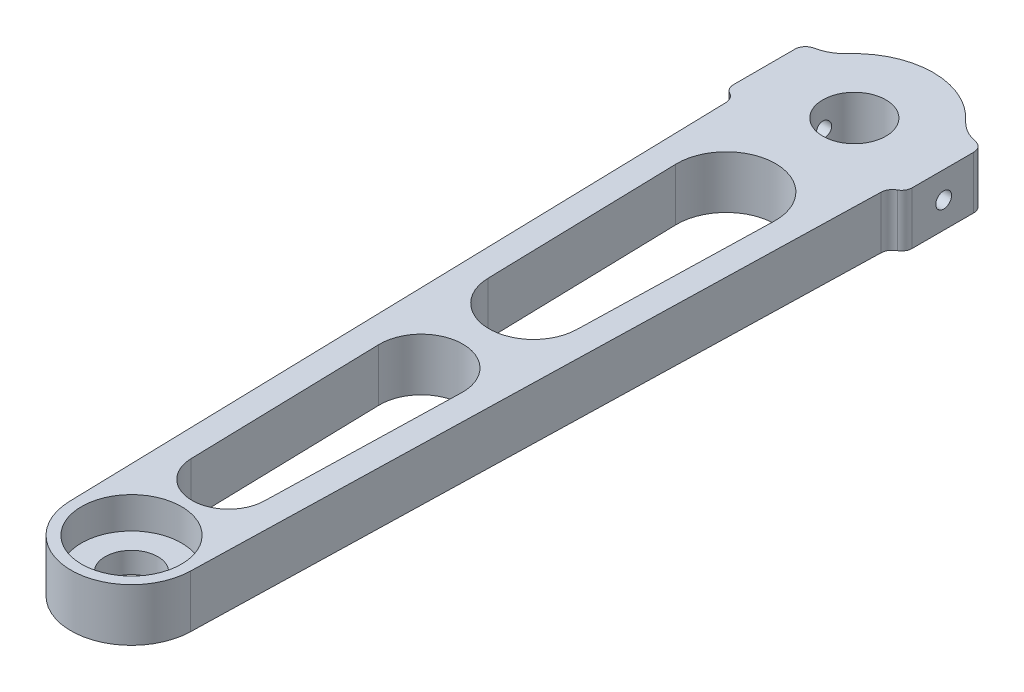
SolidWorks part; units mm, degrees
material "6061 Alloy"
ref_plane "Front Plane" through (0, 0, 0) normal (0, 0, 1) x (1, 0, 0)
ref_plane "Top Plane" through (0, 0, 0) normal (0, 1, 0) x (1, 0, 0)
ref_plane "Right Plane" through (0, 0, 0) normal (1, 0, 0) x (0, 0, -1)
sketch "Sketch1" plane through (0, 0, 0) normal (0, 1, 0) x (1, 0, 0)
  line L0 (-14.7584, -9.6805) -> (-11.4963, -137.7927)
  line L1 (14.7584, -9.6805) -> (11.4963, -137.7927)
  line L3 (-16.9951, 7.5) -> (-16.9951, -7.5)
  line L4 (16.9951, 7.5) -> (16.9951, -7.5)
  line L5 (-14.7584, -9.6805) -> (-14.9951, -0.3818) construction
  line L6 (14.7584, -9.6805) -> (14.9951, -0.3818) construction
  circle A0 centre (0, 0) radius 6
  arc A2 (-11.4963, -137.7927) -> (11.4963, -137.7927) centre (0, -137.5) ccw
  circle A3 centre (0, -137.5) radius 5
  arc A4 (-16.9951, -7.5) -> (-14.7584, -9.6805) centre (-16.9951, -9.7375) cw
  arc A5 (-16.9951, 7.5) -> (-11.2701, 9.8987) centre (-16.9951, 15.5313) ccw
  arc A8 (16.9951, 7.5) -> (11.2762, 9.8918) centre (16.9951, 15.5331) cw
  arc A9 (16.9951, -7.5) -> (14.7584, -9.6805) centre (16.9951, -9.7375) ccw
  arc A11 (14.9951, -0.3818) -> (-14.9951, -0.3818) centre (0, 0) ccw construction
  arc A12 (11.2762, 9.8918) -> (-11.2701, 9.8987) centre (0, 0) ccw
  point P14 (-16.9951, 0)
  point P25 (16.9951, 0)
  dimension "D1" = 12
  dimension "D2" = 2
  dimension "D3" = 23
  dimension "D5" = 10
  dimension "D9" = 30
  dimension "D4" = 137.5
  dimension "D7" = 15
  dimension "D8" = 15
  dimension "D11" = 2
extrude "Boss-Extrude1" add sketch "Sketch1" along normal blind 10
sketch "Sketch2" plane through (0, 10, 0) normal (0, 1, 0) x (1, 0, 0)
  circle A0 centre (0, -137.5) radius 9.5
  dimension "D1" = 19
extrude "Cut-Extrude1" cut sketch "Sketch2" against normal blind 6
sketch "Sketch4" plane through (0, 0, 0) normal (0, 1, 0) x (1, 0, 0)
  line L0 (-9.3764, -24.6182) -> (-8.4438, -61.2449)
  line L1 (9.3764, -24.6182) -> (8.4438, -61.2449)
  line L3 (-14.7584, -9.6805) -> (-11.4963, -137.7927) construction
  line L4 (0, -24.3794) -> (0, -61.0299) construction
  line L5 (-7.9005, -82.5806) -> (-6.9679, -119.2073)
  line L6 (7.9005, -82.5806) -> (6.9679, -119.2073)
  line L7 (0, -82.3794) -> (0, -119.0299) construction
  arc A0 (9.3764, -24.6182) -> (-9.3764, -24.6182) centre (0, -24.3794) ccw
  arc A1 (-8.4438, -61.2449) -> (8.4438, -61.2449) centre (0, -61.0299) ccw
  arc A2 (7.9005, -82.5806) -> (-7.9005, -82.5806) centre (0, -82.3794) ccw
  arc A3 (-6.9679, -119.2073) -> (6.9679, -119.2073) centre (0, -119.0299) ccw
  circle A5 centre (0, -137.5) radius 5 construction
  point P12 (0, -15)
  point P16 (0, -69.4764)
  point P20 (0, -74.4764)
  point P21 (0, -126)
  dimension "D1" = 15
  dimension "D2" = 5
  dimension "D3" = 11.5
  dimension "D5" = 5
extrude "Cut-Extrude3" cut sketch "Sketch4" along normal through all
fillet "Fillet1" radius 2 4 edges at (-16.9951, 5, -7.5) (-16.9951, 5, 7.5) (16.9951, 5, -7.5) (16.9951, 5, 7.5)
hole_wizard "M4 Tapped Hole1" positions "Sketch6" profile "Sketch7" tap size "M4" standard "ISO" end condition through all
sketch "Sketch6" plane through (-16.9951, 0, 0) normal (-1, 0, 0) x (0, 0, 1)
  point P0 (0, 5)
  dimension "D1" = 5
sketch "Sketch7" plane through (-16.9951, 5, 0) normal (0, 1, 0) x (0, 0, 1)
  line L0 (0, 0) -> (0, 33.9903)
  line L1 (0, 33.9903) -> (1.5, 33.9903)
  line L2 (1.5, 33.9903) -> (1.5, 0)
  line L5 (1.5, 0) -> (0, 0)
  line L11 (0, -6.35) -> (0, 107.95) construction
  dimension "Thru Tap Drill Dia." = 3
  dimension "Thru Tap Drill Depth" = 33.9903
cosmetic thread "Hole Thread1" parameters "D2"=4
